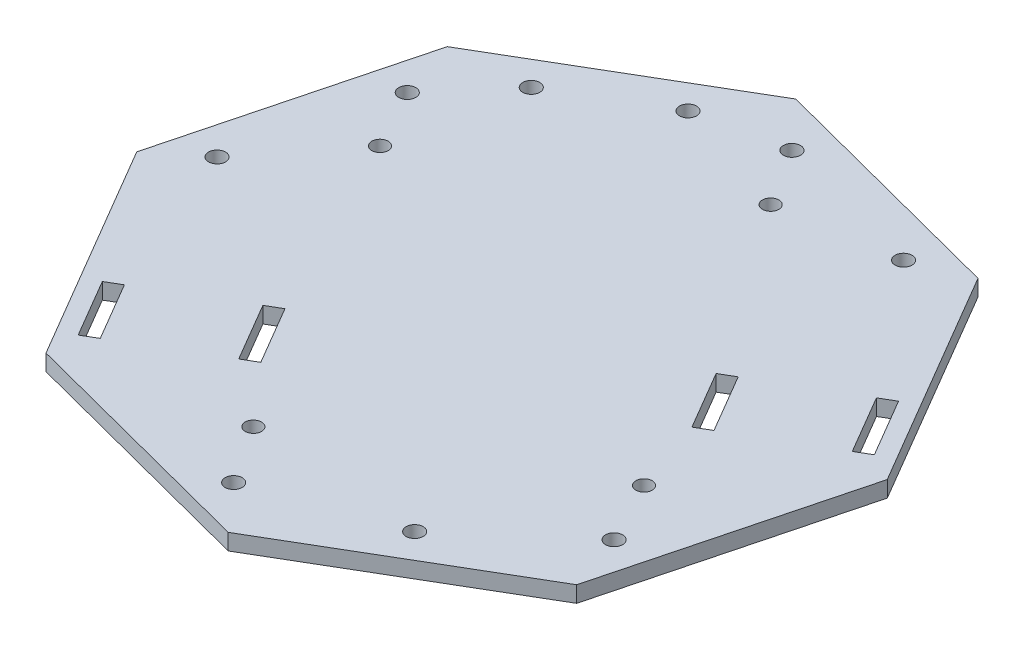
SolidWorks part; units mm, degrees
ref_plane "Front Plane" through (0, 0, 0) normal (0, 0, 1) x (1, 0, 0)
ref_plane "Top Plane" through (0, 0, 0) normal (0, 1, 0) x (1, 0, 0)
ref_plane "Right Plane" through (0, 0, 0) normal (1, 0, 0) x (0, 0, -1)
sketch "Sketch1" plane through (-113.2265, -170.1097, -309.4398) normal (0, -1, 0) x (0.8908, 0, -0.4544)
  line L0 (-0.6955, 50.8477) -> (-7.4311, -63.2537) construction
  line L1 (16.2001, -64.6487) -> (51.5924, -33.202)
  line L2 (51.5924, -33.202) -> (54.3824, 14.0603)
  line L3 (54.3824, 14.0603) -> (22.9357, 49.4527)
  line L4 (22.9357, 49.4527) -> (-24.3266, 52.2427)
  line L5 (-24.3266, 52.2427) -> (-59.719, 20.796)
  line L6 (-59.719, 20.796) -> (-62.509, -26.4664)
  line L7 (-62.509, -26.4664) -> (-31.0623, -61.8587)
  line L8 (-31.0623, -61.8587) -> (16.2001, -64.6487)
  circle A0 centre (-4.0633, -6.203) radius 57.15 construction
  dimension "D1" = 114.3
extrude "Boss-Extrude1" add sketch "Sketch1" along normal blind 3
sketch "Sketch2" plane through (0, -173.1097, 0) normal (0, -1, 0) x (1, 0, 0)
  line L0 (-163.2586, -280.5386) -> (-160.6712, -282.057)
  line L1 (-163.2586, -280.5386) -> (-156.8778, -269.6651)
  line L2 (-160.6712, -282.057) -> (-154.2904, -271.1834)
  line L3 (-156.8778, -269.6651) -> (-154.2904, -271.1834)
  line L4 (-144.4854, -291.6206) -> (-141.898, -293.1389)
  line L5 (-144.4854, -291.6206) -> (-138.0989, -280.7374)
  line L6 (-141.898, -293.1389) -> (-135.5115, -282.2557)
  line L7 (-138.0989, -280.7374) -> (-135.5115, -282.2557)
  line L8 (-135.6117, -282.4265) -> (-134.5939, -280.6921) construction
  line L9 (-137.1814, -279.1738) -> (-138.1991, -280.9081) construction
  line L10 (-138.1961, -344.6983) -> (-74.3393, -235.8799) construction
  line L11 (-63.5801, -324.414) -> (-66.1675, -322.8956)
  line L12 (-72.5484, -333.7692) -> (-66.1675, -322.8956)
  line L13 (-69.961, -335.2875) -> (-63.5801, -324.414)
  line L14 (-69.961, -335.2875) -> (-72.5484, -333.7692)
  line L15 (-82.4048, -313.4197) -> (-84.9922, -311.9014)
  line L16 (-91.3787, -322.7846) -> (-84.9922, -311.9014)
  line L17 (-88.7913, -324.3029) -> (-82.4048, -313.4197)
  line L18 (-88.7913, -324.3029) -> (-91.3787, -322.7846)
  circle A0 centre (-172.6437, -311.2558) radius 1.5875
  circle A1 centre (-165.3371, -339.3166) radius 1.5875
  circle A2 centre (-154.6358, -351.6705) radius 1.5875
  circle A3 centre (-159.2765, -328.1826) radius 1.524
  circle A4 centre (-125.8326, -271.1908) radius 1.524
  circle A5 centre (-118.6732, -260.3669) radius 1.5875
  circle A6 centre (-80.0528, -298.0553) radius 1.524
  circle A7 centre (-74.0951, -286.5262) radius 1.5875
  circle A8 centre (-136.2653, -362.4507) radius 1.5875
  circle A9 centre (-120.2611, -365.7681) radius 1.5875
  circle A10 centre (-113.4968, -355.0471) radius 1.524
  circle A11 centre (-92.2003, -358.4616) radius 1.5875
  circle A12 centre (-93.9542, -269.3056) radius 1.5875
extrude "Cut-Extrude1" cut sketch "Sketch2" against normal up to surface (3 mm away) up to face at (-119.6647, -170.1097, -313.119)
